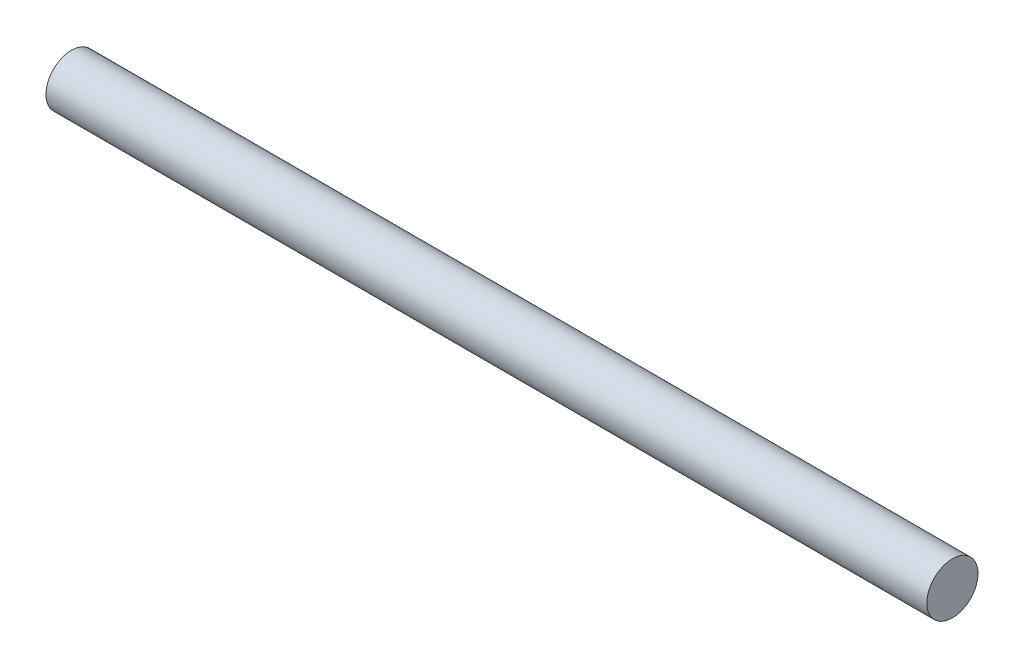
SolidWorks part; units mm, degrees
ref_plane "Plan de face" through (0, 0, 0) normal (0, 0, 1) x (1, 0, 0)
ref_plane "Plan de dessus" through (0, 0, 0) normal (0, 1, 0) x (1, 0, 0)
ref_plane "Plan de droite" through (0, 0, 0) normal (1, 0, 0) x (0, 0, -1)
sketch "Esquisse5" plane through (0, 0, 0) normal (1, 0, 0) x (0, 0, -1)
  circle A0 centre (0, 0) radius 18
extrude "Boss.-Extru.3" add sketch "Esquisse5" along normal blind 620
ref_plane "Plan2" through (10, 0, 0) normal (-1, 0, 0) x (0, 0, 1)
ref_plane "Plan4" through (610, 0, 0) normal (-1, 0, 0) x (0, 0, 1)
sketch "Esquisse6" plane through (10, 0, 0) normal (-1, 0, 0) x (0, 0, 1)
  circle A0 centre (0, 0) radius 18
sketch "Esquisse7" plane through (610, 0, 0) normal (-1, 0, 0) x (0, 0, 1)
  circle A0 centre (0, 0) radius 18
ref_plane "Plan61" through (550, 0, 0) normal (-1, 0, 0) x (0, 0, 1)
ref_plane "Plan62" through (330, 0, 0) normal (-1, 0, 0) x (0, 0, 1)
ref_plane "Plan63" through (290, 0, 0) normal (-1, 0, 0) x (0, 0, 1)
ref_plane "Plan64" through (50, 0, 0) normal (-1, 0, 0) x (0, 0, 1)
sketch "Esquisse64" plane through (550, 0, 0) normal (-1, 0, 0) x (0, 0, 1)
  circle A0 centre (0, 0) radius 18
sketch "Esquisse65" plane through (330, 0, 0) normal (-1, 0, 0) x (0, 0, 1)
  circle A0 centre (0, 0) radius 18
sketch "Esquisse66" plane through (290, 0, 0) normal (-1, 0, 0) x (0, 0, 1)
  circle A0 centre (0, 0) radius 18
sketch "Esquisse67" plane through (50, 0, 0) normal (-1, 0, 0) x (0, 0, 1)
  circle A0 centre (0, 0) radius 18
